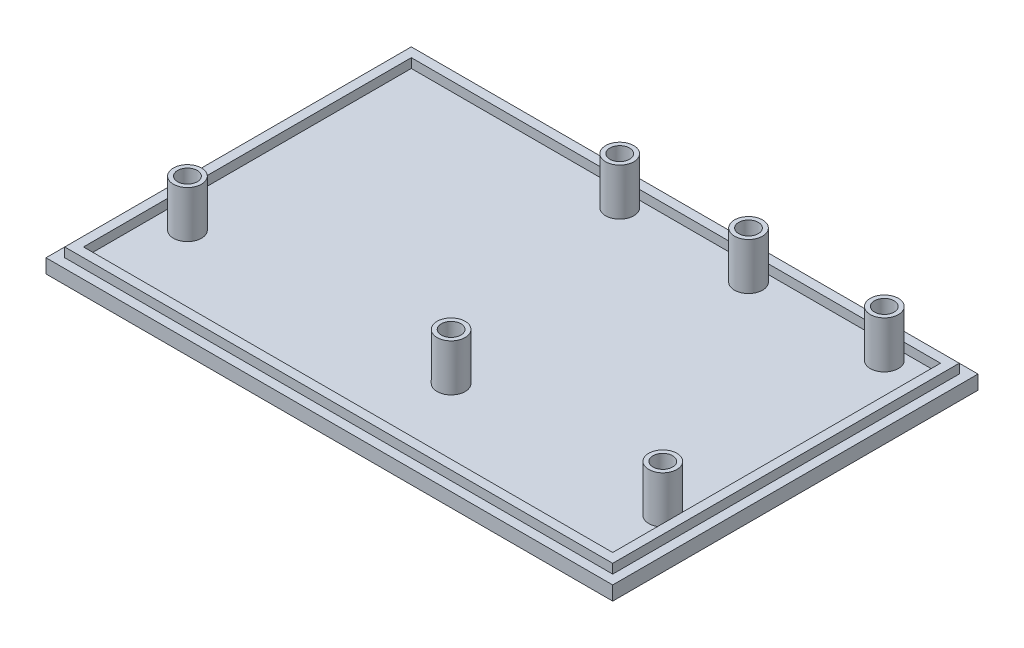
SolidWorks part; units mm, degrees
ref_plane "Front Plane" through (0, 0, 0) normal (0, 0, 1) x (1, 0, 0)
ref_plane "Top Plane" through (0, 0, 0) normal (0, 1, 0) x (1, 0, 0)
ref_plane "Right Plane" through (0, 0, 0) normal (1, 0, 0) x (0, 0, -1)
sketch "Sketch6" plane through (0, 0, 0) normal (0, 1, 0) x (1, 0, 0)
  line L1 (0, 0) -> (121, 0)
  line L2 (0, 0) -> (0, 78)
  line L3 (0, 78) -> (121, 78)
  line L4 (121, 0) -> (121, 78)
  line L9 (2, 76) -> (119, 76)
  line L10 (2, 76) -> (2, 2)
  line L11 (2, 2) -> (119, 2)
  line L12 (119, 76) -> (119, 2)
  line L13 (4, 74) -> (117, 74)
  line L14 (4, 74) -> (4, 4)
  line L15 (4, 4) -> (117, 4)
  line L16 (117, 74) -> (117, 4)
  dimension "D1" = 121
  dimension "D2" = 78
  dimension "D3" = 117
  dimension "D4" = 74
  dimension "D5" = 2
  dimension "D6" = 2
  dimension "D7" = 113
  dimension "D8" = 2
  dimension "D9" = 2
  dimension "D10" = 70
extrude "Boss-Extrude9" add sketch "Sketch6" along normal blind 3 contours L1 L4 L3 L2
sketch "Sketch14" plane through (0, 3, 0) normal (0, 1, 0) x (1, 0, 0)
  line L0 (0, -1.65) -> (0, 1.65) construction
  line L1 (2, 76) -> (119, 76)
  line L2 (2, 76) -> (2, 2)
  line L3 (2, 2) -> (119, 2)
  line L4 (119, 76) -> (119, 2)
  line L6 (0, 78) -> (121, 78) construction
  line L8 (4, 74) -> (117, 74)
  line L9 (4, 74) -> (4, 4)
  line L10 (4, 4) -> (117, 4)
  line L11 (117, 74) -> (117, 4)
  dimension "D1" = 117
  dimension "D2" = 2
  dimension "D3" = 74
  dimension "D4" = 2
  dimension "D5" = 113
  dimension "D6" = 70
  dimension "D7" = 2
  dimension "D8" = 2
extrude "Boss-Extrude11" add sketch "Sketch14" along normal blind 2
sketch "Sketch16" plane through (0, 3, 0) normal (0, 1, 0) x (1, 0, 0)
  line L0 (4, 74) -> (4, 4) construction
  line L1 (117, 74) -> (4, 74) construction
  circle A0 centre (52, 70.5) radius 2.1
  circle A1 centre (52, 70.5) radius 3
  dimension "D1" = 48
  dimension "D2" = 3.5
  dimension "D3" = 6
  dimension "D4" = 4.2
extrude "Boss-Extrude12" add sketch "Sketch16" along normal blind 10
sketch "Sketch17" plane through (0, 3, 0) normal (0, 1, 0) x (1, 0, 0)
  line L0 (117, 4) -> (117, 74) construction
  line L1 (117, 74) -> (4, 74) construction
  circle A1 centre (108.5, 70.5) radius 2.1
  circle A3 centre (108.5, 70.5) radius 3
  point P0 (108.5, 70.5)
  dimension "D1" = 8.5
  dimension "D2" = 3.5
extrude "Boss-Extrude13" add sketch "Sketch17" along normal blind 10 contours A3 | A1
sketch "Sketch18" plane through (0, 3, 0) normal (0, 1, 0) x (1, 0, 0)
  line L0 (117, 74) -> (4, 74) construction
  line L1 (117, 4) -> (117, 74) construction
  circle A0 centre (79.5, 70.5) radius 2.1
  circle A1 centre (79.5, 70.5) radius 3
  point P0 (79.5, 70.5)
  dimension "D1" = 3.5
  dimension "D2" = 37.5
extrude "Boss-Extrude14" add sketch "Sketch18" along normal blind 10
sketch "Sketch19" plane through (0, 3, 0) normal (0, 1, 0) x (1, 0, 0)
  line L0 (4, 74) -> (4, 4) construction
  line L1 (4, 4) -> (117, 4) construction
  circle A0 centre (10, 20.2) radius 2.1
  circle A1 centre (10, 20.2) radius 3
  point P0 (10, 20.2)
  dimension "D1" = 6
  dimension "D2" = 16.2
extrude "Boss-Extrude15" add sketch "Sketch19" along normal blind 10 contours A1 | A0
sketch "Sketch20" plane through (0, 3, 0) normal (0, 1, 0) x (1, 0, 0)
  line L0 (117, 4) -> (117, 74) construction
  line L1 (4, 4) -> (117, 4) construction
  circle A0 centre (113.5, 18.2) radius 2.1
  circle A1 centre (113.5, 18.2) radius 3
  point P0 (113.5, 18.2)
  dimension "D1" = 3.5
  dimension "D2" = 14.2
extrude "Boss-Extrude16" add sketch "Sketch20" along normal blind 10
sketch "Sketch21" plane through (0, 3, 0) normal (0, 1, 0) x (1, 0, 0)
  line L0 (4, 4) -> (117, 4) construction
  line L1 (117, 4) -> (117, 74) construction
  circle A0 centre (66.5, 20) radius 2.1
  circle A1 centre (66.5, 20) radius 3
  point P0 (66.5, 20)
  dimension "D1" = 16
  dimension "D2" = 50.5
extrude "Boss-Extrude17" add sketch "Sketch21" along normal blind 10
sketch "Sketch22" plane through (0, 0, 0) normal (0, -1, 0) x (-1, 0, 0)
  text T0 "54"
extrude "Cut-Extrude2" cut sketch "Sketch22" against normal blind 1 from surface at 0 starting at face at (60.5, 0, -39)
